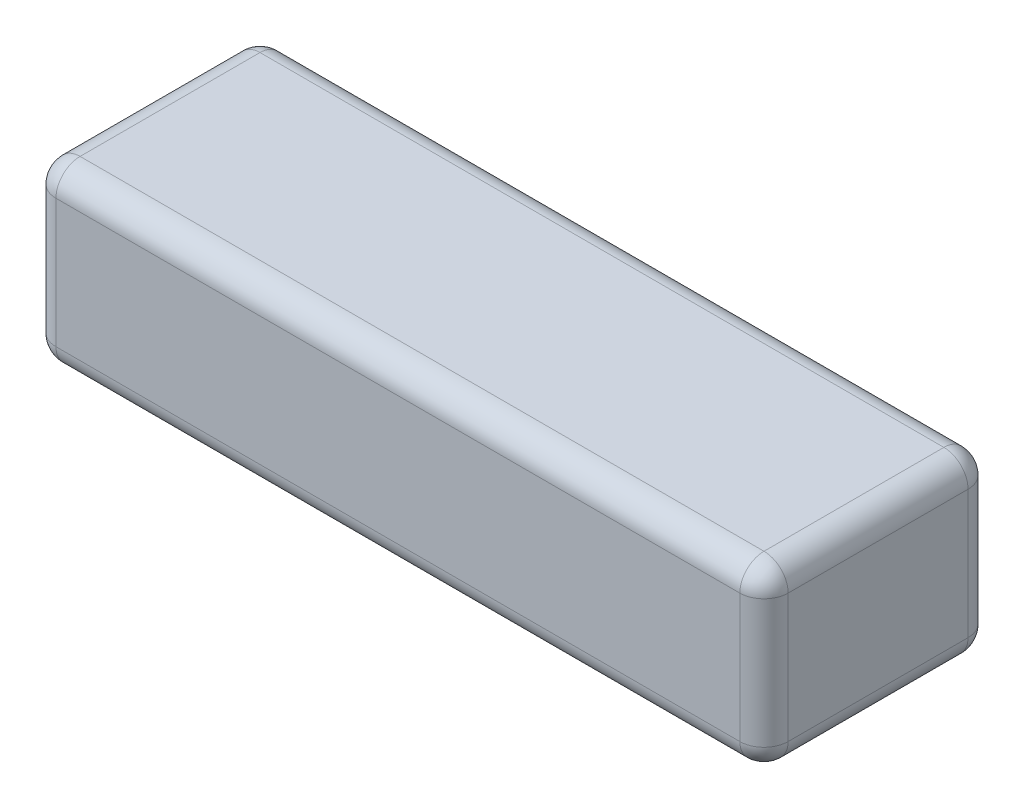
SolidWorks part; units mm, degrees
ref_plane "Front Plane" through (0, 0, 0) normal (0, 0, 1) x (1, 0, 0)
ref_plane "Top Plane" through (0, 0, 0) normal (0, 1, 0) x (1, 0, 0)
ref_plane "Right Plane" through (0, 0, 0) normal (1, 0, 0) x (0, 0, -1)
sketch "Sketch1" plane through (0, 0, 0) normal (0, 1, 0) x (1, 0, 0)
  line L1 (-77, 24) -> (77, 24)
  line L2 (-77, 24) -> (-77, -24)
  line L3 (-77, -24) -> (77, -24)
  line L4 (77, 24) -> (77, -24)
  line L5 (-77, 24) -> (77, -24) construction
  line L6 (-77, -24) -> (77, 24) construction
  point P0 (0, 0)
  dimension "D1" = 154
  dimension "D2" = 48
extrude "Boss-Extrude1" add sketch "Sketch1" along normal blind 37.2
fillet "Fillet1" radius 5.08 12 edges at (-77, 18.6, -24) (-77, 18.6, 24) (77, 18.6, 24) (77, 18.6, -24) (0, 0, -24) (-77, 0, 0) (0, 0, 24) (77, 0, 0) (0, 37.2, 24) (-77, 37.2, 0) (0, 37.2, -24) (77, 37.2, 0)
